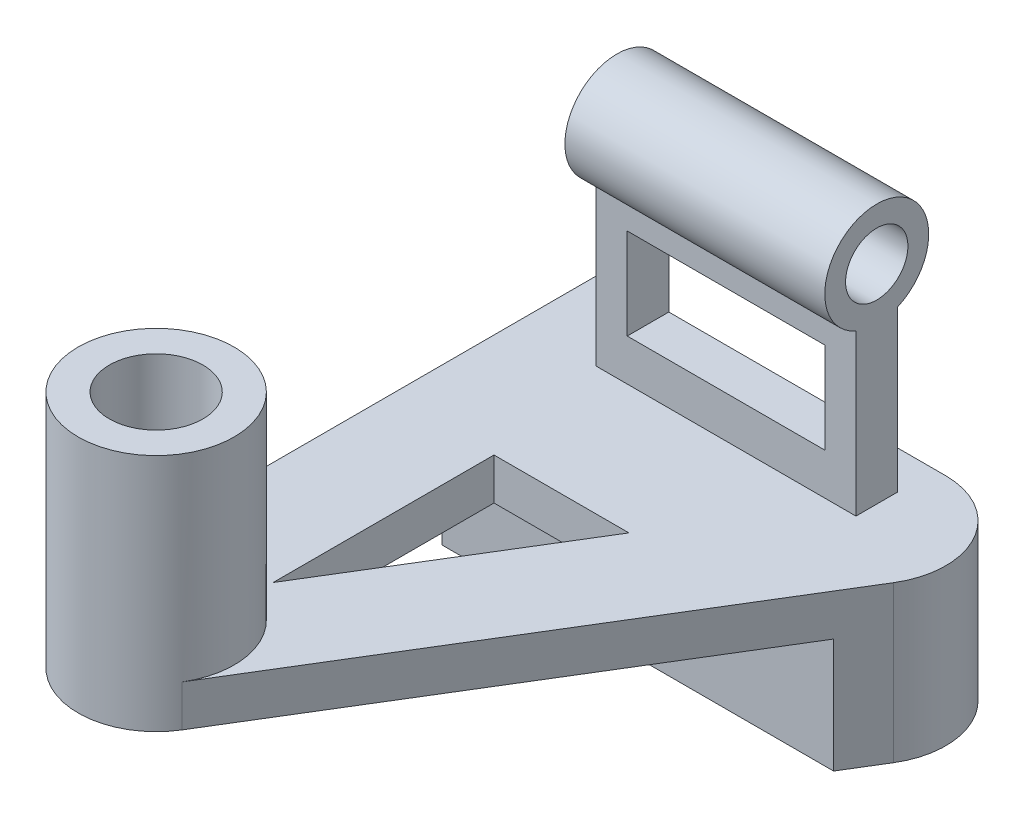
SolidWorks part; units mm, degrees
material "Plain Carbon Steel"
ref_plane "Front Plane" through (0, 0, 0) normal (0, 0, 1) x (1, 0, 0)
ref_plane "Top Plane" through (0, 0, 0) normal (0, 1, 0) x (1, 0, 0)
ref_plane "Right Plane" through (0, 0, 0) normal (1, 0, 0) x (0, 0, -1)
sketch "Sketch1" plane through (0, 0, 0) normal (0, 1, 0) x (1, 0, 0)
  line L0 (0, -54.6087) -> (0, 45.3913)
  line L1 (0, 45.3913) -> (66.9179, 45.3913)
  line L2 (79.7189, 22.5725) -> (27.801, -62.4275)
  arc A0 (0, -54.6087) -> (27.801, -62.4275) centre (15, -54.6087) ccw
  arc A1 (66.9179, 45.3913) -> (79.7189, 22.5725) centre (66.9179, 30.3913) cw
  point P6 (0, -107.9433)
  point P9 (93.6566, 45.3913)
  point P10 (80, 37.7302)
  point P11 (0, 0)
  dimension "D3" = 15
  dimension "D1" = 80
  dimension "D2" = 100
extrude "Base triangle" add sketch "Sketch1" along normal blind 8
sketch "Sketch2" plane through (0, 8, 0) normal (0, 1, 0) x (1, 0, 0)
  line L0 (0, 45.3913) -> (0, -54.6087) construction
  line L1 (15, 38.026) -> (65, 38.026)
  line L2 (15, 38.026) -> (15, 30.026)
  line L3 (15, 30.026) -> (65, 30.026)
  line L4 (65, 38.026) -> (65, 30.026)
  line L5 (15, 38.026) -> (65, 30.026) construction
  line L6 (15, 30.026) -> (65, 38.026) construction
  point P0 (40, 34.026)
  dimension "D1" = 8
  dimension "D2" = 50
  dimension "D3" = 15
extrude "Rectangle Block" add sketch "Sketch2" along normal blind 38
sketch "Sketch3" plane through (0, 0, -30.026) normal (0, 0, 1) x (1, 0, 0)
  line L0 (65, 46) -> (65, 8) construction
  line L1 (21, 34) -> (59, 34)
  line L2 (21, 34) -> (21, 16)
  line L3 (21, 16) -> (59, 16)
  line L4 (59, 34) -> (59, 16)
  line L5 (21, 34) -> (59, 16) construction
  line L6 (21, 16) -> (59, 34) construction
  line L7 (15, 46) -> (15, 8) construction
  line L8 (15, 8) -> (65, 8) construction
  point P0 (40, 25)
  dimension "D1" = 6
  dimension "D2" = 6
  dimension "D3" = 8
  dimension "D4" = 18
extrude "Cut-Extrude2" cut sketch "Sketch3" against normal up to next contours L2 L1 L4 L3
sketch "Sketch4" plane through (15, 0, 0) normal (-1, 0, 0) x (0, 0, 1)
  line L4 (-38.026, 8) -> (-30.026, 8)
  line L5 (-30.026, 8) -> (-30.026, 46)
  line L6 (-30.026, 46) -> (-38.026, 46)
  line L7 (-38.026, 46) -> (-38.026, 8)
  line L8 (-38.026, 8) -> (-30.026, 8)
  line L9 (-30.026, 8) -> (-30.026, 46)
  line L10 (-30.026, 46) -> (-38.026, 46)
  line L11 (-38.026, 46) -> (-38.026, 8)
  circle A0 centre (-34.026, 55.1652) radius 10
  point P6 (-34.026, 46)
  line M8 (-30.026, 46) -> (-38.026, 46)
  dimension "D2" = 20
  dimension "D1" = 0
extrude "Cyinder Block" add sketch "Sketch4" against normal up to vertex (50 mm away) contours A0 M8 up to point (65, 46, -38.026)
sketch "Sketch5" plane through (15, 0, 0) normal (-1, 0, 0) x (0, 0, 1)
  circle A0 centre (-34.026, 55.1652) radius 6
  dimension "D1" = 12
extrude "Cut-Extrude3" cut sketch "Sketch5" against normal up to next contours A0
ref_plane "Plane3" through (65, 0, 0) normal (1, 0, 0) x (0, 0, -1)
sketch "Sketch9" plane through (65, 0, 0) normal (1, 0, 0) x (0, 0, -1)
  line L6 (30.026, 8) -> (38.026, 8)
  line L7 (38.026, 8) -> (38.026, 38.8348)
  line L8 (30.026, 38.8348) -> (30.026, 8)
  arc A2 (38.026, 38.8348) -> (30.026, 38.8348) centre (34.026, 48) ccw
  point P4 (0, 0)
  point P5 (0, 0)
  point P7 (0, 0)
  dimension "D1" = 40
extrude "Boss-Extrude5" add sketch "Sketch9" against normal blind 50
sketch "Sketch10" plane through (65, 0, 0) normal (1, 0, 0) x (0, 0, -1)
  line L3 (30.026, 38.8348) -> (30.026, 8)
  line L4 (30.026, 8) -> (38.026, 8)
  line L5 (38.026, 8) -> (38.026, 38.8348)
  arc A1 (43.3622, 51.5826) -> (24.6897, 51.5826) centre (34.026, 48) ccw
  arc A3 (43.3622, 51.5826) -> (24.6897, 51.5826) centre (34.026, 55.1652) ccw
  arc A4 (24.6897, 51.5826) -> (30.026, 38.8348) centre (34.026, 48) ccw
  arc A5 (38.026, 38.8348) -> (43.3622, 51.5826) centre (34.026, 48) ccw
  arc A6 (43.3622, 51.5826) -> (24.6897, 51.5826) centre (34.026, 55.1652) ccw
  dimension "D1" = 0
extrude "Cut-Extrude4" cut sketch "Sketch10" against normal blind 50
sketch "Sketch11" plane through (65, 0, 0) normal (1, 0, 0) x (0, 0, -1)
  line L3 (30.026, 38.8348) -> (30.026, 8)
  line L4 (30.026, 8) -> (38.026, 8)
  line L5 (38.026, 8) -> (38.026, 38.8348)
  line L6 (30.026, 38.8348) -> (30.026, 8)
  line L7 (30.026, 8) -> (38.026, 8)
  line L8 (38.026, 8) -> (38.026, 38.8348)
  circle A0 centre (34.026, 48) radius 6
  arc A1 (38.026, 38.8348) -> (30.026, 38.8348) centre (34.026, 48) ccw
  arc A2 (38.026, 38.8348) -> (30.026, 38.8348) centre (34.026, 48) ccw
  dimension "D2" = 12
  dimension "D1" = 0
extrude "Cut-Extrude5" cut sketch "Sketch11" against normal blind 50 contours A0
sketch "Sketch12" plane through (0, 0, -30.026) normal (0, 0, 1) x (1, 0, 0)
  line L0 (65, -11) -> (65, 11) construction
  line L1 (21, 33.5077) -> (59, 33.5077)
  line L2 (21, 33.5077) -> (21, 16)
  line L3 (21, 16) -> (59, 16)
  line L4 (59, 33.5077) -> (59, 16)
  line L5 (21, 33.5077) -> (59, 16) construction
  line L6 (21, 16) -> (59, 33.5077) construction
  line L7 (15, 38.8348) -> (15, 8) construction
  line L8 (27.801, 8) -> (79.7189, 8) construction
  point P0 (40, 24.7539)
  dimension "D1" = 6
  dimension "D2" = 6
  dimension "D3" = 8
extrude "Cut-Extrude6" cut sketch "Sketch12" against normal up to next
ref_plane "Plane4" through (0, 8, 0) normal (0, 1, 0) x (1, 0, 0)
sketch "Sketch13" plane through (0, 8, 0) normal (0, 1, 0) x (1, 0, 0)
  arc A0 (0, -54.6087) -> (27.801, -62.4275) centre (15, -54.6087) ccw construction
  arc A2 (0, -54.6087) -> (27.801, -62.4275) centre (15, -54.6087) ccw
  circle A4 centre (15, -54.6087) radius 15
extrude "Boss-Extrude6" add sketch "Sketch13" along normal blind 38 contours A2 A4
sketch "Sketch14" plane through (0, 46, 0) normal (0, 1, 0) x (1, 0, 0)
  circle A1 centre (15, -54.6087) radius 9
  dimension "D2" = 18
extrude "Cut-Extrude7" cut sketch "Sketch14" against normal up to next
sketch "Sketch15" plane through (0, 8, 0) normal (0, 1, 0) x (1, 0, 0)
  line L0 (20, -37.1087) -> (20, 5.3913)
  line L1 (20, 5.3913) -> (45.959, 5.3913)
  line L2 (45.959, 5.3913) -> (20, -37.1087)
  line L3 (27.801, -62.4275) -> (79.7189, 22.5725)
  line L4 (66.9179, 45.3913) -> (0, 45.3913)
  line L5 (0, 45.3913) -> (0, -54.6087)
  line L6 (27.801, -62.4275) -> (79.7189, 22.5725)
  line L7 (66.9179, 45.3913) -> (0, 45.3913)
  line L8 (0, 45.3913) -> (0, -54.6087)
  arc A2 (27.801, -62.4275) -> (0, -54.6087) centre (15, -54.6087) ccw
  arc A3 (79.7189, 22.5725) -> (66.9179, 45.3913) centre (66.9179, 30.3913) ccw
  arc A4 (27.801, -62.4275) -> (0, -54.6087) centre (15, -54.6087) ccw
  arc A5 (79.7189, 22.5725) -> (66.9179, 45.3913) centre (66.9179, 30.3913) ccw
  point P8 (0, 0)
  dimension "D2" = 20
  dimension "D3" = 40
  dimension "D4" = 42.5
  dimension "D1" = 0
extrude "Cut-Extrude9" cut sketch "Sketch15" against normal up to next contours L2 L0 L1
ref_plane "Plane7" through (0, 0, 0) normal (0, -1, 0) x (-1, 0, 0)
sketch "Sketch20" plane through (0, 0, 0) normal (0, -1, 0) x (-1, 0, 0)
  line L0 (-75.3327, 15.3913) -> (0, 15.3913)
  line L1 (-27.801, -62.4275) -> (-79.7189, 22.5725) construction
  line L2 (0, 45.3913) -> (0, -54.6087) construction
  line L3 (-66.9179, 45.3913) -> (0, 45.3913) construction
  line L7 (0, 45.3913) -> (-66.9179, 45.3913)
  line L8 (-79.7189, 22.5725) -> (-27.801, -62.4275)
  line L9 (0, -54.6087) -> (0, 45.3913)
  line L10 (0, 45.3913) -> (-66.9179, 45.3913)
  line L11 (-79.7189, 22.5725) -> (-75.3327, 15.3913)
  line L12 (0, 15.3913) -> (0, 45.3913)
  arc A2 (-66.9179, 45.3913) -> (-79.7189, 22.5725) centre (-66.9179, 30.3913) ccw
  arc A3 (-27.801, -62.4275) -> (0, -54.6087) centre (-15, -54.6087) ccw
  arc A4 (-66.9179, 45.3913) -> (-79.7189, 22.5725) centre (-66.9179, 30.3913) ccw
  dimension "D1" = 30
  dimension "D2" = 0
extrude "Boss-Extrude7" add sketch "Sketch20" along normal blind 22
